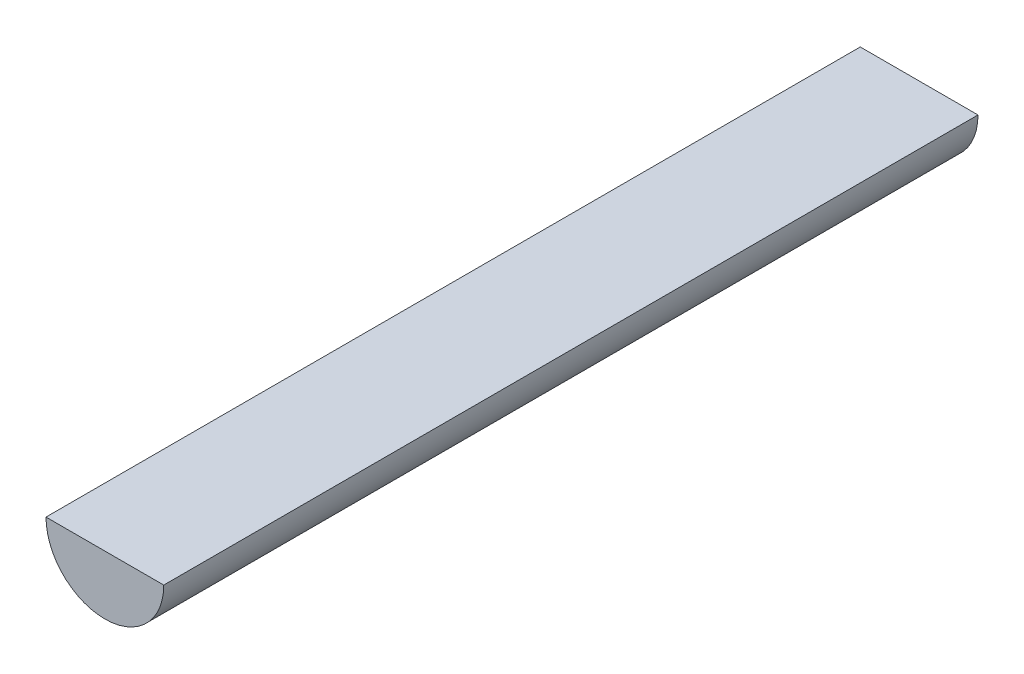
SolidWorks part; units mm, degrees
ref_plane "Front Plane" through (0, 0, 0) normal (0, 0, 1) x (1, 0, 0)
ref_plane "Top Plane" through (0, 0, 0) normal (0, 1, 0) x (1, 0, 0)
ref_plane "Right Plane" through (0, 0, 0) normal (1, 0, 0) x (0, 0, -1)
sketch "Sketch1" plane through (0, 0, 0) normal (0, 0, 1) x (1, 0, 0)
  line L0 (-4.7, 0) -> (4.7, 0)
  arc A0 (-4.7, 0) -> (4.7, 0) centre (0, 0) ccw
  dimension "D1" = 4.7
extrude "Boss-Extrude1" add sketch "Sketch1" along normal blind 65
